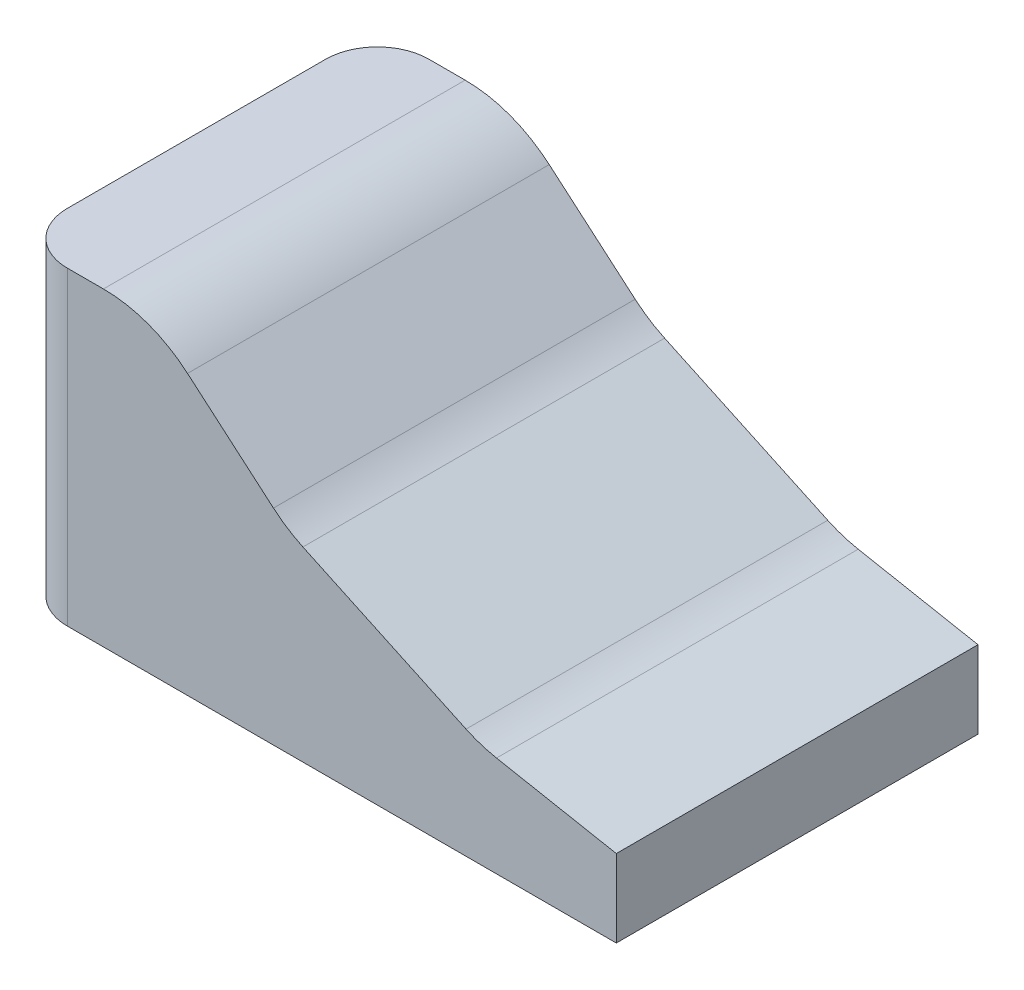
SolidWorks part; units mm, degrees
ref_plane "Front Plane" through (0, 0, 0) normal (0, 0, 1) x (1, 0, 0)
ref_plane "Top Plane" through (0, 0, 0) normal (0, 1, 0) x (1, 0, 0)
ref_plane "Right Plane" through (0, 0, 0) normal (1, 0, 0) x (0, 0, -1)
sketch "Sketch1" plane through (0, 0, 0) normal (0, 0, 1) x (1, 0, 0)
  line L0 (0, 152.4) -> (0, 0)
  line L1 (0, 0) -> (295.275, 0)
  line L2 (295.275, 0) -> (295.275, 38.1)
  line L3 (295.275, 38.1) -> (228.6, 50.8)
  line L4 (228.6, 50.8) -> (133.35, 95.25)
  line L5 (133.35, 95.25) -> (66.675, 152.4)
  line L6 (66.675, 152.4) -> (0, 152.4)
  dimension "D1" = 228.6
  dimension "D2" = 295.275
  dimension "D3" = 152.4
  dimension "D4" = 38.1
  dimension "D5" = 133.35
  dimension "D6" = 50.8
  dimension "D7" = 95.25
  dimension "D8" = 66.675
extrude "Extrude1" add sketch "Sketch1" against normal blind 177.8
fillet "Fillet1" radius 63.5 3 edges at (228.6, 50.8, -88.9) (133.35, 95.25, -88.9) (66.675, 152.4, -88.9)
fillet "Fillet2" radius 25.4 2 edges at (0, 76.2, -177.8) (0, 76.2, 0)
